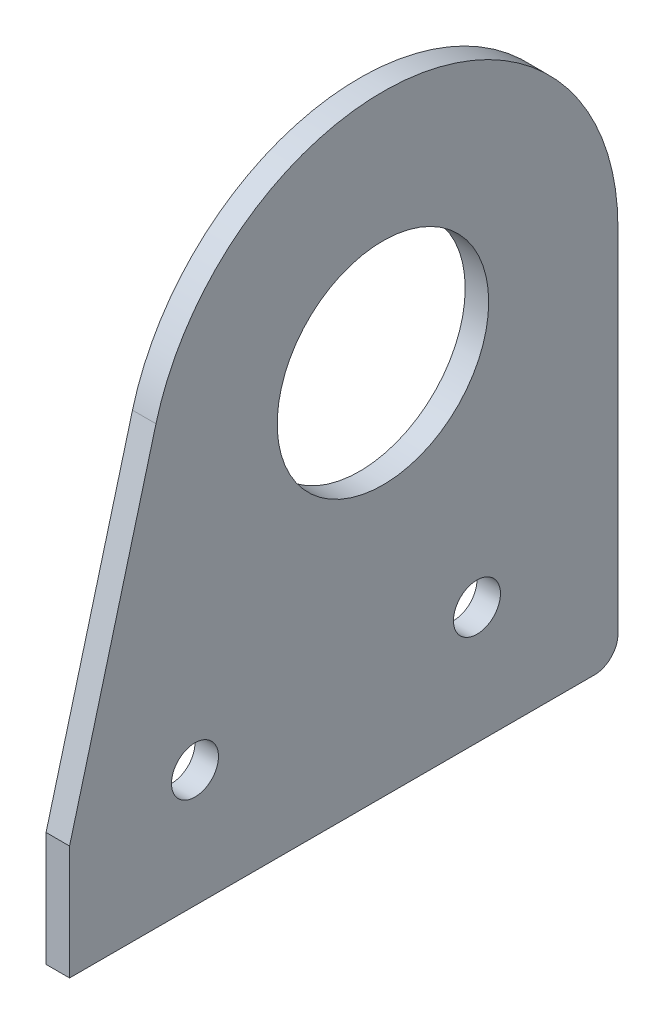
SolidWorks part; units mm, degrees
ref_plane "Front Plane" through (0, 0, 0) normal (0, 0, 1) x (1, 0, 0)
ref_plane "Top Plane" through (0, 0, 0) normal (0, 1, 0) x (1, 0, 0)
ref_plane "Right Plane" through (0, 0, 0) normal (1, 0, 0) x (0, 0, -1)
sketch "Sketch2" plane through (0, 0, 0) normal (1, 0, 0) x (0, 0, -1)
  line L0 (-168.275, 19.05) -> (-64.7217, 19.05) construction
  line L1 (-4.292, -28.2508) -> (89.7471, -42.5375) construction
  line L2 (-171.45, 22.225) -> (-171.45, 41.275) construction
  line L3 (-168.275, 44.45) -> (-101.6, 44.45) construction
  line L4 (-30.6681, 154.2675) -> (-42.3441, 110.6923)
  line L5 (41.6129, 175.1877) -> (218.62, -77.6046) construction
  line L6 (15.0515, 157.8062) -> (118.3631, 25.535) construction
  line L7 (53.6439, -14.125) -> (-17.3081, 137.9762) construction
  line L8 (-4.6354, 18.5275) -> (78.6163, 39.3564) construction
  line L9 (80.5683, -35.188) -> (-3.6594, -18.7447) construction
  line L10 (96.725, 25.2801) -> (96.9473, 25.8909) construction
  line L11 (55, 0) -> (-55, 0) construction
  line L12 (-20.2056, -20.2056) -> (-55.7414, 15.3303) construction
  line L13 (0, 95.25) -> (255.6229, 95.25) construction
  line L14 (0, 50.8) -> (255.6229, 50.8) construction
  line L15 (122.3804, 3.2387) -> (110.5619, -30.0732) construction
  line L16 (31.75, 146.05) -> (31.75, 110.6081)
  line L17 (94.5769, 26.062) -> (94.7992, 26.6728) construction
  line L18 (98.8732, 24.4983) -> (99.0955, 25.1091) construction
  line L19 (68.3924, -14.8897) -> (67.8097, -15.722) construction
  line L21 (66.5198, -13.5785) -> (65.9371, -14.4108) construction
  line L22 (92.6084, -23.7036) -> (92.5198, -24.7158) construction
  line L23 (94.8857, -23.9029) -> (94.7971, -24.915) construction
  line L26 (96.9473, 25.8909) -> (68.3924, -14.8897) construction
  line L27 (96.9473, 25.8909) -> (92.6084, -23.7036) construction
  line L28 (88.26, 2.0227) -> (96.9473, 25.8909) construction
  line L29 (-95.25, 50.8) -> (-95.25, 83.8035) construction
  line L30 (-69.8795, 95.25) -> (-51.3544, 95.25) construction
  line L31 (-71.523, 95.0336) -> (-90.5435, 89.9371) construction
  line L32 (0, 0) -> (87.8872, 2.3014) construction
  line L33 (0, 146.05) -> (88.26, 2.0227) construction
  line L34 (31.75, 110.6081) -> (31.75, 98.425)
  line L35 (33.6435, 106.0845) -> (117.7963, 23.1789) construction
  line L36 (-45.2207, 99.9565) -> (-45.4109, 99.2468) construction
  line L37 (-42.3441, 95.25) -> (28.575, 95.25)
  line L38 (0, 55) -> (0, -55) construction
  line L39 (-42.3441, 95.25) -> (-42.3441, 110.6923)
  circle A0 centre (0, 146.05) radius 14.2875
  circle A1 centre (0, 0) radius 14.2875 construction
  circle A2 centre (0, 146.05) radius 50.8 construction
  circle A3 centre (0, 0) radius 50.8 construction
  circle A5 centre (-57.15, 31.75) radius 3.556 construction
  circle A6 centre (-82.55, 31.75) radius 3.556 construction
  circle A7 centre (-107.95, 31.75) radius 3.556 construction
  circle A8 centre (-133.35, 31.75) radius 3.556 construction
  circle A9 centre (-158.75, 31.75) radius 3.556 construction
  arc A10 (31.75, 146.05) -> (-30.6681, 154.2675) centre (0, 146.05) ccw
  arc A11 (-171.45, 41.275) -> (-168.275, 44.45) centre (-168.275, 41.275) cw construction
  arc A12 (-168.275, 19.05) -> (-171.45, 22.225) centre (-168.275, 22.225) cw construction
  arc A14 (-55.7414, 15.3303) -> (-64.7217, 19.05) centre (-64.7217, 6.35) ccw construction
  arc A15 (-4.6354, 18.5275) -> (-3.6594, -18.7447) centre (0, 0) ccw construction
  arc A16 (15.0515, 157.8062) -> (-17.3081, 137.9762) centre (0, 146.05) ccw construction
  arc A17 (53.6439, -14.125) -> (118.3631, 25.535) centre (88.26, 2.0227) ccw construction
  arc A18 (80.5683, -35.188) -> (78.6163, 39.3564) centre (87.8872, 2.3014) ccw construction
  circle A19 centre (87.8872, 2.3014) radius 32 construction
  circle A20 centre (88.26, 2.0227) radius 32 construction
  circle A21 centre (88.26, 2.0227) radius 24.75 construction
  circle A24 centre (87.8872, 2.3014) radius 24.75 construction
  arc A29 (-20.2056, -20.2056) -> (-4.292, -28.2508) centre (0, 0) ccw construction
  arc A30 (122.3804, 3.2387) -> (117.7963, 23.1789) centre (104.4268, 9.6083) ccw construction
  arc A31 (89.7471, -42.5375) -> (110.5619, -30.0732) centre (92.6084, -23.7036) ccw construction
  circle A32 centre (88.26, 2.0227) radius 14.2875 construction
  circle A33 centre (87.8872, 2.3014) radius 14.2875 construction
  arc A34 (94.5769, 26.062) -> (98.8732, 24.4983) centre (96.725, 25.2801) ccw construction
  arc A35 (99.0955, 25.1091) -> (94.7992, 26.6728) centre (96.9473, 25.8909) ccw construction
  arc A37 (65.9371, -14.4108) -> (66.4985, -17.5946) centre (67.8097, -15.722) ccw construction
  arc A38 (94.8857, -23.9029) -> (92.8076, -21.4263) centre (92.6084, -23.7036) ccw construction
  arc A39 (92.3206, -26.9931) -> (94.7971, -24.915) centre (92.5198, -24.7158) ccw construction
  arc A40 (69.7036, -13.0172) -> (92.8076, -21.4263) centre (96.9473, 25.8909) ccw construction
  arc A41 (66.4985, -17.5946) -> (92.3206, -26.9931) centre (96.9473, 25.8909) ccw construction
  arc A42 (69.7036, -13.0172) -> (66.5198, -13.5785) centre (68.3924, -14.8897) ccw construction
  circle A43 centre (-82.55, 57.15) radius 3.556 construction
  circle A44 centre (-82.55, 82.55) radius 3.556 construction
  arc A45 (-51.3544, 95.25) -> (-45.2207, 99.9565) centre (-51.3544, 101.6) ccw construction
  arc A46 (-95.25, 50.8) -> (-101.6, 44.45) centre (-101.6, 50.8) cw construction
  arc A48 (-90.5435, 89.9371) -> (-95.25, 83.8035) centre (-88.9, 83.8035) ccw construction
  arc A49 (-71.523, 95.0336) -> (-69.8795, 95.25) centre (-69.8795, 88.9) cw construction
  arc A50 (33.6435, 106.0845) -> (31.75, 110.6081) centre (38.1, 110.6081) cw construction
  arc A51 (28.575, 95.25) -> (31.75, 98.425) centre (28.575, 98.425) ccw
  arc A52 (-45.4109, 99.2468) -> (-42.3441, 95.25) centre (-42.3441, 98.425) ccw construction
  circle A53 centre (-25.4, 111.125) radius 3.175
  circle A54 centre (12.7, 111.125) radius 3.175
  point P50 (96.8362, 25.5855)
  point P76 (-95.25, 88.676)
  point P79 (102.7469, -16.3909)
  point P97 (-70.7155, 95.25)
  point P105 (31.75, 95.25)
  point P113 (31.75, 107.95)
  dimension "D1" = 28.575
  dimension "D2" = 101.6
  dimension "D3" = 44.45
  dimension "D4" = 19.05
  dimension "D6" = 57.15
  dimension "D8" = 7.112
  dimension "D14" = 105
  dimension "D15" = 3.175
  dimension "D16" = 12.7
  dimension "D18" = 38.1972
  dimension "D19" = 76.3944
  dimension "D20" = 520
  dimension "D21" = 360
  dimension "D22" = 64
  dimension "D23" = 49.5
  dimension "D24" = 4.572
  dimension "D25" = 19.05
  dimension "D26" = 31.75
  dimension "D27" = 25.4
  dimension "D28" = 2.286
  dimension "D29" = 1.016
  dimension "D36" = 25.4
  dimension "D38" = 12.7
  dimension "D39" = 6.35
  dimension "D40" = 15
  dimension "D42" = 6.35
  dimension "D43" = 5.588
  dimension "D44" = 58.5
  dimension "D47" = 31.75
  dimension "D48" = 12.7
  dimension "D50" = 6.35
  dimension "D51" = 3.175
  dimension "D52" = 38.1
  dimension "D55" = 6.35
  dimension "D5" = 135
  dimension "D7" = 12.7
  dimension "D9" = 57.15
  dimension "D10" = 12.7
  dimension "D12" = 25.4
  dimension "D13" = 12.7
  dimension "D17" = 55
  dimension "D30" = 3
  dimension "D31" = 30
  dimension "D32" = 15
  dimension "D33" = 50.8
  dimension "D34" = 50.8
  dimension "D35" = 1.016
  dimension "D37" = 12.7
  dimension "D41" = 25.4
  dimension "D45" = 1.5
  dimension "D46" = 110
  dimension "D49" = 12.7
  dimension "D53" = 12.7
  dimension "D54" = 15.875
  dimension "D11" = 5
extrude "Boss-Extrude1" add sketch "Sketch2" along normal blind 3.175
